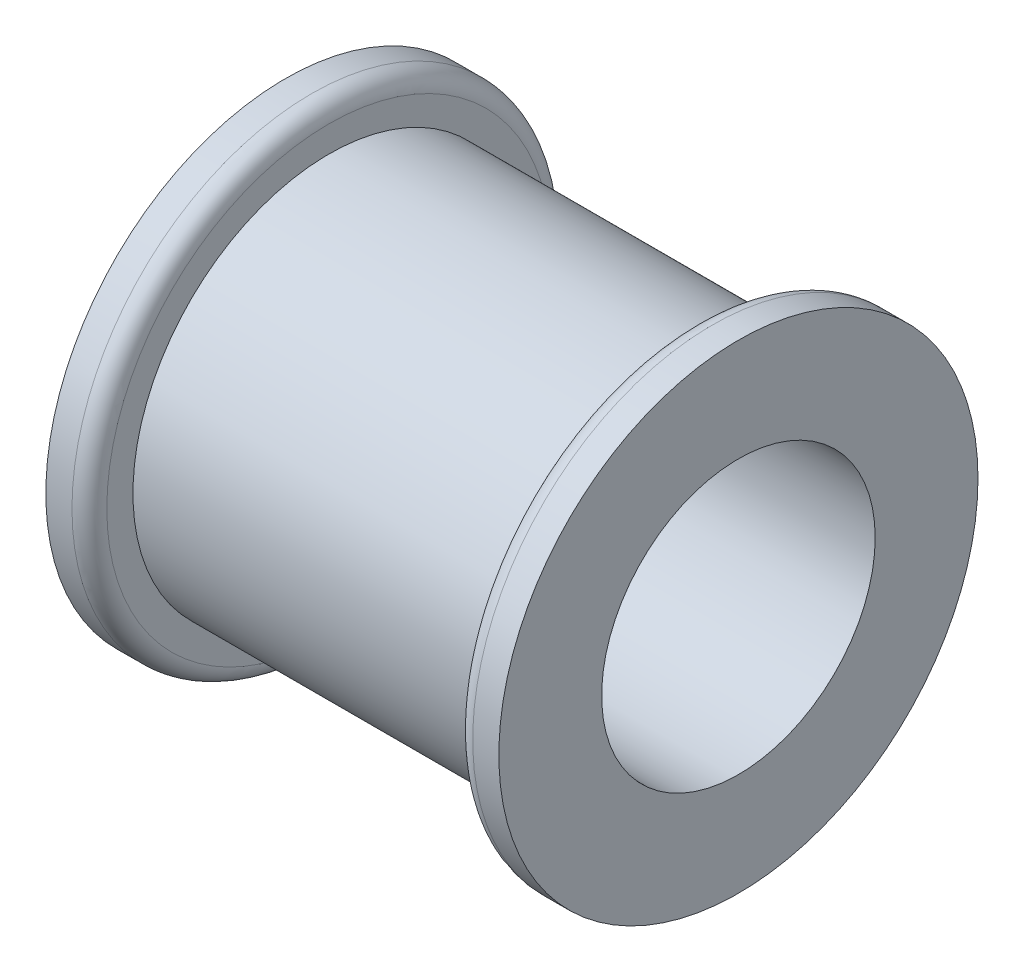
SolidWorks part; units mm, degrees
ref_plane "Front" through (0, 0, 0) normal (0, 0, 1) x (1, 0, 0)
ref_plane "Top" through (0, 0, 0) normal (0, 1, 0) x (1, 0, 0)
ref_plane "Right" through (0, 0, 0) normal (1, 0, 0) x (0, 0, -1)
sketch "Sketch1" plane through (0, 0, 0) normal (1, 0, 0) x (0, 0, -1)
  circle A0 centre (0, 0) radius 9.9695
  circle A1 centre (0, 0) radius 14.2875
  dimension "D1" = 28.575
  dimension "D2" = 19.939
extrude "Boss-Extrude1" add sketch "Sketch1" along normal blind 26.67
ref_plane "Mid_Plane" through (13.335, 0, 0) normal (-1, 0, 0) x (0, 0, 1)
sketch "Sketch2" plane through (26.67, 0, 0) normal (1, 0, 0) x (0, 0, -1)
  circle A0 centre (0, 0) radius 9.9695 construction
  circle A1 centre (0, 0) radius 9.9695
  circle A2 centre (0, 0) radius 17.4625
  dimension "D1" = 34.925
extrude "Boss-Extrude2" add sketch "Sketch2" along normal blind 3.175
fillet "Fillet1" radius 1.27 1 edges at (26.67, 0, -17.4625)
mirror "Mirror1" about plane through (13.335, 0, 0) normal (-1, 0, 0) of "Fillet1", "Boss-Extrude2"
